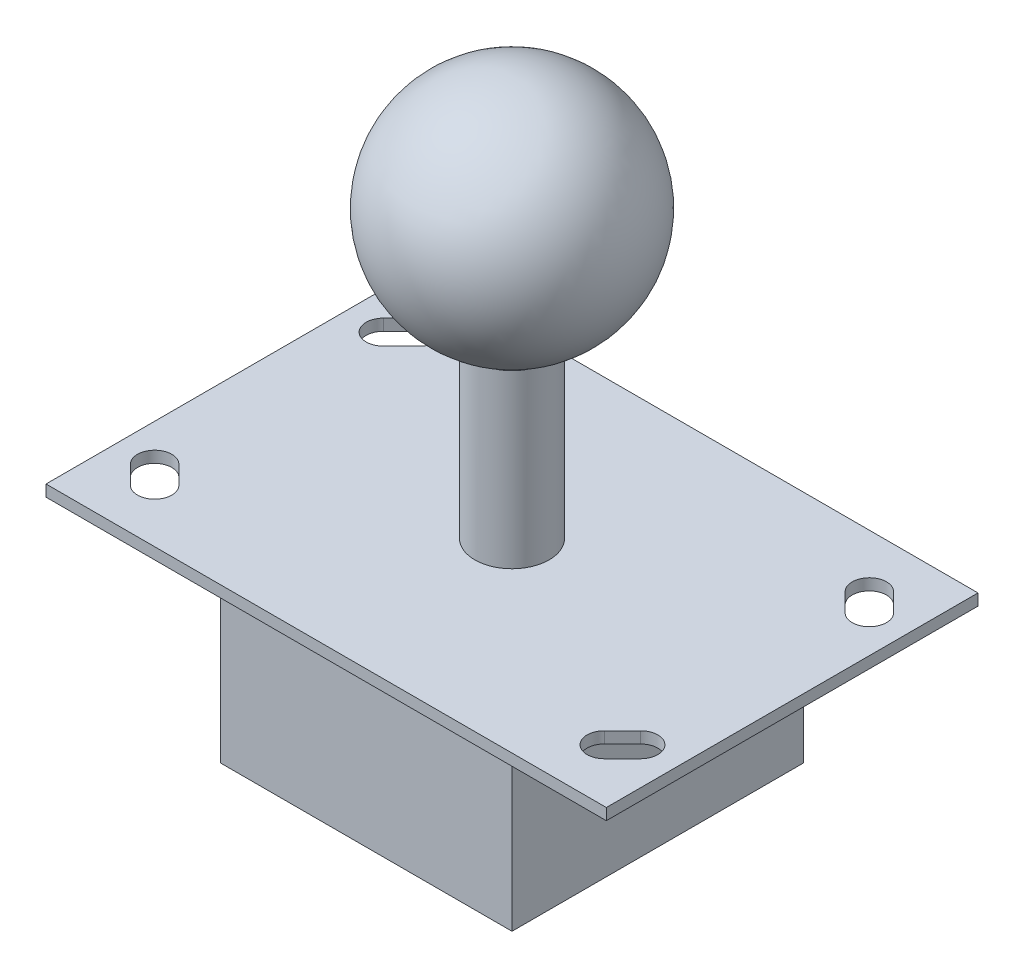
SolidWorks part; units mm, degrees
ref_plane "Front Plane" through (0, 0, 0) normal (0, 0, 1) x (1, 0, 0)
ref_plane "Top Plane" through (0, 0, 0) normal (0, 1, 0) x (1, 0, 0)
ref_plane "Right Plane" through (0, 0, 0) normal (1, 0, 0) x (0, 0, -1)
sketch "Sketch3" plane through (0, 0, 0) normal (0, 1, 0) x (1, 0, 0)
  circle A0 centre (0, 0) radius 6.5
  dimension "D1" = 13
extrude "Boss-Extrude2" add sketch "Sketch3" along normal blind 30
sketch "Sketch4" plane through (0, 0, 0) normal (0, -1, 0) x (-1, 0, 0)
  line L1 (-49, 32.5) -> (49, 32.5)
  line L2 (-49, 32.5) -> (-49, -32.5)
  line L3 (-49, -32.5) -> (49, -32.5)
  line L4 (49, 32.5) -> (49, -32.5)
  point P4 (49, 0)
  point P6 (0, 32.5)
  dimension "D1" = 98
  dimension "D2" = 65
extrude "Boss-Extrude3" add sketch "Sketch4" along normal blind 2
sketch "Sketch5" plane through (0, -2, 0) normal (0, -1, 0) x (1, 0, 0)
  line L1 (-25.5, 25.5) -> (25.5, 25.5)
  line L2 (-25.5, 25.5) -> (-25.5, -25.5)
  line L3 (-25.5, -25.5) -> (25.5, -25.5)
  line L4 (25.5, 25.5) -> (25.5, -25.5)
  point P4 (0, 25.5)
  point P6 (25.5, 0)
  dimension "D1" = 51
  dimension "D2" = 51
extrude "Boss-Extrude4" add sketch "Sketch5" along normal blind 32
sketch "Sketch7" plane through (0, 0, 0) normal (0, 1, 0) x (1, 0, 0)
  line L0 (-44.6213, 22.1213) -> (-41.4393, 25.3033)
  line L1 (-40.3787, 17.8787) -> (-37.1967, 21.0607)
  line L2 (-49, -32.5) -> (-49, 32.5) construction
  line L3 (-49, 32.5) -> (49, 32.5) construction
  line L4 (-49, 0) -> (49, 0) construction
  line L5 (49, 32.5) -> (49, -32.5) construction
  line L6 (0, 32.5) -> (0, -32.5) construction
  line L7 (49, -32.5) -> (-49, -32.5) construction
  line L8 (-44.6213, -22.1213) -> (-41.4393, -25.3033)
  line L9 (-40.3787, -17.8787) -> (-37.1967, -21.0607)
  line L10 (40.3787, -17.8787) -> (37.1967, -21.0607)
  line L11 (44.6213, -22.1213) -> (41.4393, -25.3033)
  line L12 (44.6213, 22.1213) -> (41.4393, 25.3033)
  line L13 (40.3787, 17.8787) -> (37.1967, 21.0607)
  line L14 (-44.6213, 17.8787) -> (-37.1967, 25.3033) construction
  arc A0 (-37.1967, 21.0607) -> (-41.4393, 25.3033) centre (-39.318, 23.182) ccw
  arc A1 (-44.6213, 22.1213) -> (-40.3787, 17.8787) centre (-42.5, 20) ccw
  arc A2 (-37.1967, -21.0607) -> (-41.4393, -25.3033) centre (-39.318, -23.182) cw
  arc A3 (-44.6213, -22.1213) -> (-40.3787, -17.8787) centre (-42.5, -20) cw
  arc A4 (37.1967, -21.0607) -> (41.4393, -25.3033) centre (39.318, -23.182) ccw
  arc A5 (44.6213, -22.1213) -> (40.3787, -17.8787) centre (42.5, -20) ccw
  arc A6 (37.1967, 21.0607) -> (41.4393, 25.3033) centre (39.318, 23.182) cw
  arc A7 (44.6213, 22.1213) -> (40.3787, 17.8787) centre (42.5, 20) cw
  point P36 (-40.909, 21.591)
  point P37 (0, 0)
  point P40 (0, 0)
  point P41 (-40.909, 21.591)
  dimension "D1" = 6
  dimension "D2" = 4.5
  dimension "D3" = 42.5
  dimension "D4" = 20
  dimension "D5" = 4.5
  dimension "D6" = 45
extrude "Cut-Extrude1" cut sketch "Sketch7" against normal through all
sketch3d "3DSketch1"
  line L0 (0, 30, 0) -> (0, 70, 0) construction
  line L1 (0, 30, 0) -> (0, 0, 0) construction
  line L2 (0, 70, 0) -> (0, 30, 0)
  arc A0 (0, 70, 0) -> (0, 30, 0) centre (0, 50, 0) ccw
  point P6 (0, 50, 20)
  dimension "D1" = 40
  dimension "D2" = 20
revolve "Revolve3" add sketch "3DSketch1" angle 360 about L0
